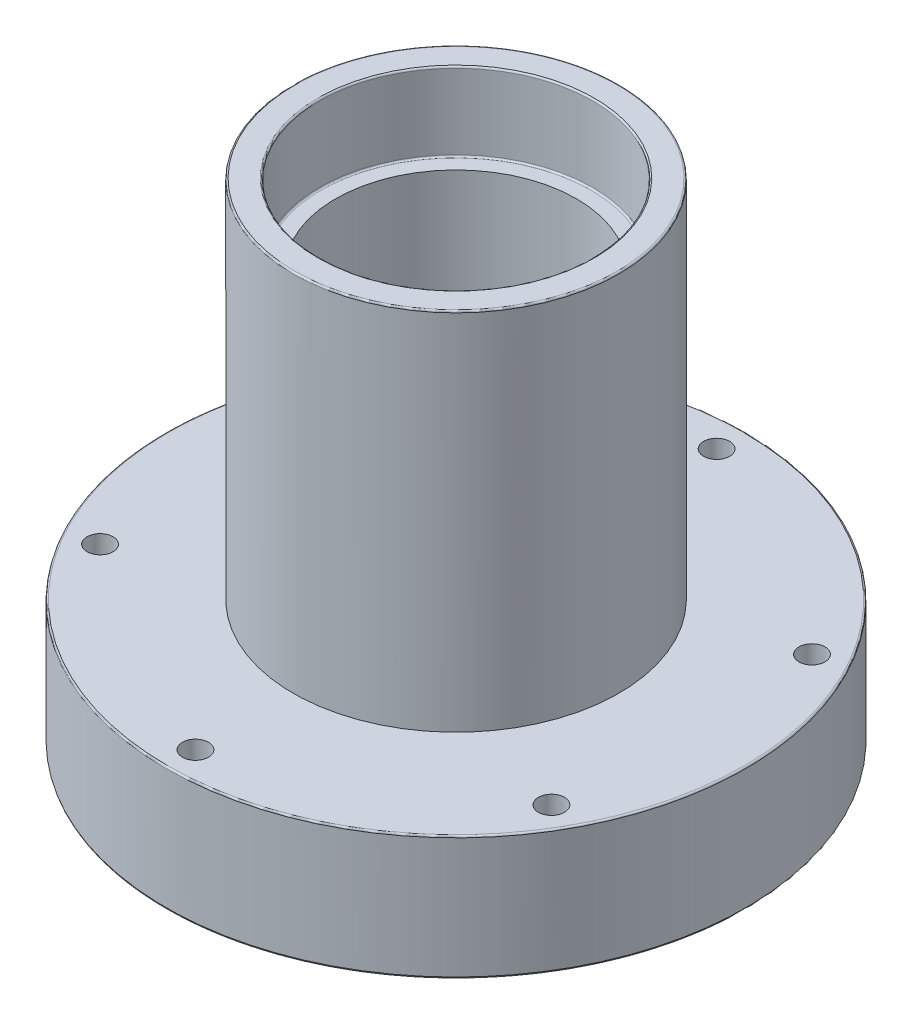
SolidWorks part; units mm, degrees
material "6061 Alloy"
ref_plane "Front Plane" through (0, 0, 0) normal (0, 0, 1) x (1, 0, 0)
ref_plane "Top Plane" through (0, 0, 0) normal (0, 1, 0) x (1, 0, 0)
ref_plane "Right Plane" through (0, 0, 0) normal (1, 0, 0) x (0, 0, -1)
sketch "Sketch1" plane through (0, 0, 0) normal (1, 0, 0) x (0, 0, -1)
  line L0 (21, 0) -> (21, 12)
  line L1 (21, 12) -> (18.5, 12)
  line L2 (18.5, 12) -> (18.5, 63)
  line L3 (18.5, 63) -> (21, 63)
  line L4 (21, 63) -> (21, 75)
  line L5 (21, 75) -> (25, 75)
  line L6 (25, 75) -> (25, 19)
  line L7 (25, 19) -> (44.5, 19)
  line L8 (44.5, 19) -> (44.5, 0)
  line L10 (0, -1000.2373) -> (0, 48999.7627) construction
  line L13 (21, 0) -> (44.5, 0)
  dimension "D1" = 19
  dimension "D2" = 12
  dimension "D3" = 42
  dimension "D4" = 50
  dimension "D5" = 75
  dimension "D7" = 37
  dimension "D8" = 89
revolve "Revolve1" add sketch "Sketch1" angle 360 about L10
sketch "Sketch2" plane through (0, 19, 0) normal (0, 1, 0) x (1, 0, 0)
  circle A0 centre (0, 40) radius 2
  circle A1 centre (34.641, 20) radius 2
  circle A2 centre (34.641, -20) radius 2
  circle A3 centre (0, -40) radius 2
  circle A4 centre (-34.641, -20) radius 2
  circle A5 centre (-34.641, 20) radius 2
  point P16 (0, 0)
  dimension "D1" = 4
  dimension "D2" = 40
  dimension "D4" = 40
  dimension "D3" = 6
extrude "Cut-Extrude1" cut sketch "Sketch2" against normal through all
fillet "Fillet1" radius 0.25 6 edges at (0, 19, -44.5) (0, 0, -44.5) (0, 75, -25) (0, 75, -21) (0, 63, -21) (0, 12, -21)
